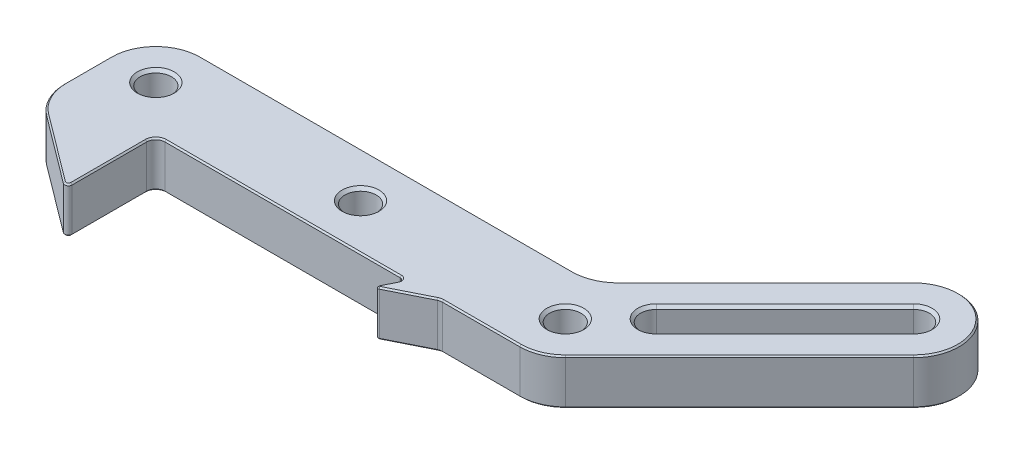
SolidWorks part; units mm, degrees
ref_plane "Front Plane" through (0, 0, 0) normal (0, 0, 1) x (1, 0, 0)
ref_plane "Top Plane" through (0, 0, 0) normal (0, 1, 0) x (1, 0, 0)
ref_plane "Right Plane" through (0, 0, 0) normal (1, 0, 0) x (0, 0, -1)
sketch "Sketch1" plane through (0, 0, 0) normal (0, 1, 0) x (1, 0, 0)
  line L0 (6.35, 6.35) -> (24.3105, 24.3105) construction
  line L1 (4.8065, 7.8935) -> (22.767, 25.854)
  line L2 (7.8935, 4.8065) -> (25.854, 22.767)
  line L3 (-50.8, -7.62) -> (-50.8, -18.034)
  line L4 (-49.53, -6.35) -> (-16.697, -6.35)
  line L5 (4.4901, -4.4902) -> (28.8008, 19.8206)
  line L6 (28.8008, 28.8005) -> (28.8005, 28.8008)
  line L7 (19.8206, 28.8008) -> (-0.7705, 8.2098)
  line L8 (-5.2604, 6.35) -> (-57.1503, 6.35)
  line L9 (-63.5, 0.0003) -> (-63.5, -6.3501)
  line L10 (-60.9601, -11.4299) -> (-51.6128, -18.4404)
  line L11 (-16.2426, -7.0852) -> (-17.1217, -8.8434)
  line L12 (-16.7809, -9.1842) -> (-11.3807, -6.4841)
  line L13 (-10.8127, -6.35) -> (0.0001, -6.35)
  circle A0 centre (0, 0) radius 2.1828
  arc A1 (4.8065, 7.8935) -> (7.8935, 4.8065) centre (6.35, 6.35) ccw
  arc A2 (25.854, 22.767) -> (22.767, 25.854) centre (24.3105, 24.3105) ccw
  arc A3 (28.8005, 28.8008) -> (19.8206, 28.8008) centre (24.3105, 24.3109) ccw
  arc A4 (28.8008, 19.8206) -> (28.8008, 28.8005) centre (24.3109, 24.3105) ccw
  arc A5 (0.0001, -6.35) -> (4.4901, -4.4902) centre (0.0001, -0.0003) ccw
  arc A6 (-0.7705, 8.2098) -> (-5.2604, 6.35) centre (-5.2604, 12.6997) cw
  arc A7 (-63.5, -6.3501) -> (-60.9601, -11.4299) centre (-57.1503, -6.3501) ccw
  arc A8 (-57.1503, 6.35) -> (-63.5, 0.0003) centre (-57.1503, 0.0003) ccw
  arc A9 (-50.8, -7.62) -> (-49.53, -6.35) centre (-49.53, -7.62) cw
  arc A10 (-50.8, -18.034) -> (-51.6128, -18.4404) centre (-51.308, -18.034) cw
  circle A11 centre (-57.1503, 0.0003) radius 2.1828
  circle A12 centre (-28.575, 0.0003) radius 2.1828
  arc A13 (-16.2426, -7.0852) -> (-16.697, -6.35) centre (-16.697, -6.858) ccw
  arc A14 (-17.1217, -8.8434) -> (-16.7809, -9.1842) centre (-16.8945, -8.957) ccw
  arc A15 (-11.3807, -6.4841) -> (-10.8127, -6.35) centre (-10.8127, -7.62) cw
  point P5 (15.3303, 15.3303)
  point P29 (-63.5, -9.525)
  point P32 (-63.5, 6.35)
  point P35 (-50.8, -6.35)
  point P38 (-50.8, -19.05)
  point P48 (-15.875, -6.35)
  point P51 (-17.4625, -9.525)
  point P54 (-11.1125, -6.35)
  dimension "D1" = 4.3656
  dimension "D4" = 2.1828
  dimension "D16" = 6.3497
  dimension "D17" = 1.27
  dimension "D18" = 0.508
  dimension "D20" = 4.3656
  dimension "D21" = 4.3656
  dimension "D26" = 0.508
  dimension "D27" = 0.254
  dimension "D28" = 1.27
  dimension "D2" = 6.35
  dimension "D3" = 6.35
  dimension "D5" = 25.4
  dimension "D6" = 50.8
  dimension "D7" = 6.35
  dimension "D8" = 17.9605
  dimension "D9" = 12.7
  dimension "D10" = 6.35
  dimension "D11" = 6.35
  dimension "D12" = 6.35
  dimension "D13" = 6.35
  dimension "D14" = 15.875
  dimension "D15" = 12.7
  dimension "D19" = 28.575
  dimension "D22" = 12.7
  dimension "D23" = 4.7625
  dimension "D24" = 1.5875
  dimension "D25" = 3.175
extrude "Boss-Extrude1" add sketch "Sketch1" along normal blind 6.35
chamfer "Chamfer2" distance 0.3969 angle 45 14 edges at (-57.1503, 0, 2.1826) (-57.1503, 6.35, 2.1826) (-28.575, 0, 2.1826) (-28.575, 6.35, 2.1826) (0, 0, 2.1828) (0, 6.35, 2.1828) (16.8737, 6.35, -13.7868) (25.854, 6.35, -25.854) (4.8065, 6.35, -4.8065) (13.7868, 6.35, -16.8737) (16.8737, 0, -13.7868) (25.854, 0, -25.854) (4.8065, 0, -4.8065) (13.7868, 0, -16.8737)
chamfer "Chamfer3" distance 0.1984 angle 45 44 edges at (-56.2865, 0, 14.9352) (-51.0808, 0, 18.4884) (-62.8296, 0, 9.1898) (-50.8, 0, 12.827) (-63.5, 0, 3.1749) (-50.428, 0, 6.722) (-61.6402, 0, -4.4902) (-33.1135, 0, 6.35) (-31.2053, 0, -6.35) (-16.2648, 0, 6.5909) (-2.8305, 0, -6.8333) (-16.6822, 0, 7.9643) (9.5251, 0, -18.5053) (-17.0741, 0, 9.1366) (24.3105, 0, -30.6606) (-14.0808, 0, 7.8342) (28.8006, 0, -28.8006) (-11.1045, 0, 6.384) (30.6606, 0, -24.3105) (-5.4063, 0, 6.35) (16.6454, 0, -7.6652) (2.43, 0, 5.8667) (-61.6402, 6.35, -4.4902) (-63.5, 6.35, 3.1749) (-31.2053, 6.35, -6.35) (-62.8296, 6.35, 9.1898) (-2.8305, 6.35, -6.8333) (-56.2865, 6.35, 14.9352) (9.5251, 6.35, -18.5053) (-51.0808, 6.35, 18.4884) (24.3105, 6.35, -30.6606) (-50.8, 6.35, 12.827) (28.8006, 6.35, -28.8006) (-50.428, 6.35, 6.722) (30.6606, 6.35, -24.3105) (-33.1135, 6.35, 6.35) (16.6454, 6.35, -7.6652) (-16.2648, 6.35, 6.5909) (2.43, 6.35, 5.8667) (-16.6822, 6.35, 7.9643) (-5.4063, 6.35, 6.35) (-17.0741, 6.35, 9.1366) (-11.1045, 6.35, 6.384) (-14.0808, 6.35, 7.8342)
